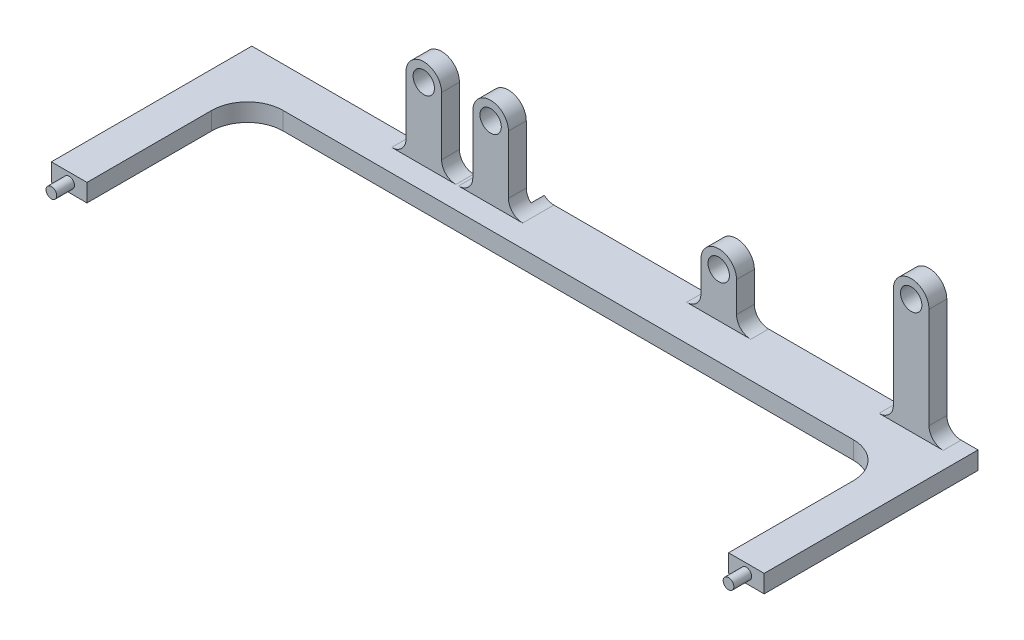
SolidWorks part; units mm, degrees
material "Alloy Steel"
ref_plane "Front Plane" through (0, 0, 0) normal (0, 0, 1) x (1, 0, 0)
ref_plane "Top Plane" through (0, 0, 0) normal (0, 1, 0) x (1, 0, 0)
ref_plane "Right Plane" through (0, 0, 0) normal (1, 0, 0) x (0, 0, -1)
sketch "Sketch1" plane through (0, 0, 0) normal (0, 1, 0) x (1, 0, 0)
  line L0 (-173.4223, 480) -> (-173.4223, 450)
  line L1 (-173.4223, 480) -> (800, 480)
  line L2 (-800, 450) -> (-800, -450)
  line L3 (-173.4223, -480) -> (800, -480)
  line L4 (800, 480) -> (800, -480)
  line L5 (0, 0) -> (800, -480) construction
  line L6 (-750, -450) -> (800, 480) construction
  line L7 (-173.4223, 450) -> (-800, 450)
  line L9 (0, 0) -> (-1738.6087, 0) construction
  line L11 (-173.4223, -450) -> (-800, -450)
  line L12 (-173.4223, -480) -> (-173.4223, -450)
  point P0 (0, 0)
  dimension "D1" = 960
  dimension "D3" = 30
extrude "Boss-Extrude1" add sketch "Sketch1" against normal blind 40
sketch "Sketch2" plane through (0, 0, 480) normal (0, 0, 1) x (1, 0, 0)
  line L0 (298, 0) -> (298, 100)
  line L1 (-173.4223, 0) -> (800, 0) construction
  line L2 (218, 0) -> (218, 100)
  line L3 (730, 0) -> (730, 258.2)
  line L4 (650, 0) -> (650, 258.2)
  line L5 (800, -40) -> (800, 0) construction
  arc A0 (218, 100) -> (298, 100) centre (258, 100) cw
  arc A1 (650, 258.2) -> (730, 258.2) centre (690, 258.2) cw
  circle A2 centre (258, 100) radius 24
  circle A3 centre (690, 258.2) radius 24
  dimension "D1" = 40
  dimension "D2" = 40
  dimension "D6" = 48
  dimension "D7" = 48
  dimension "D3" = 70
  dimension "D4" = 432
  dimension "D5" = 158.2
  dimension "D8" = 100
extrude "Boss-Extrude2" add sketch "Sketch2" against normal blind 40
sketch "Sketch3" plane through (0, 0, 450) normal (0, 0, 1) x (1, 0, 0)
  line L6 (-184, 0) -> (-184, 162.7)
  line L7 (-264, 0) -> (-264, 162.7)
  line L8 (-334, 0) -> (-334, 162.7)
  line L9 (-414, 0) -> (-414, 162.7)
  arc A4 (-264, 162.7) -> (-184, 162.7) centre (-224, 162.7) cw
  circle A5 centre (-224, 162.7) radius 24
  arc A6 (-414, 162.7) -> (-334, 162.7) centre (-374, 162.7) cw
  circle A7 centre (-374, 162.7) radius 24
  dimension "D11" = 150
  dimension "D12" = 48
  dimension "D13" = 40
mirror "Mirror1" about plane through (0, 0, 0) normal (0, 0, 1) of bodies 102
extrude "Boss-Extrude3" add sketch "Sketch3" against normal blind 40
mirror "Mirror2" about plane through (0, 0, 0) normal (0, 0, 1) of "Boss-Extrude3"
scale "Scale1" scale about centroid uniform scaling yes scale factor 0.125
fillet "Fillet3" radius 4 8 edges at (100.696, -9.9224, -57.5) (46.696, -9.9224, -57.5) (-13.554, -9.9224, -53.75) (-32.304, -9.9224, -53.75) (100.696, -9.9224, 57.5) (46.696, -9.9224, 57.5) (-13.554, -9.9224, 53.75) (-32.304, -9.9224, 53.75)
fillet "Fillet4" radius 4 8 edges at (-3.554, -9.9224, -53.75) (-22.304, -9.9224, -53.75) (56.696, -9.9224, -57.5) (110.696, -9.9224, -57.5) (110.696, -9.9224, 57.5) (56.696, -9.9224, 57.5) (-3.554, -9.9224, 53.75) (-22.304, -9.9224, 53.75)
sketch "Sketch4" plane through (0, -9.9224, 0) normal (0, 1, 0) x (1, 0, 0)
  line L0 (-70.554, 0) -> (109.446, 0) construction
  line L1 (-60.554, 45) -> (99.446, 45)
  line L2 (-70.554, 35) -> (-70.554, -35)
  line L3 (-60.554, -45) -> (99.446, -45)
  line L4 (109.446, 35) -> (109.446, -35)
  line L5 (119.446, -60) -> (119.446, 60) construction
  line L6 (-80.554, 56.25) -> (-80.554, -56.25) construction
  arc A0 (99.446, 45) -> (109.446, 35) centre (99.446, 35) cw
  arc A1 (99.446, -45) -> (109.446, -35) centre (99.446, -35) ccw
  arc A2 (-70.554, -35) -> (-60.554, -45) centre (-60.554, -35) ccw
  arc A3 (-60.554, 45) -> (-70.554, 35) centre (-60.554, 35) ccw
  point P8 (119.446, 0)
  point P9 (19.446, 0)
  point P12 (109.446, 45)
  point P17 (-70.554, -45)
  point P20 (-70.554, 45)
  dimension "D3" = 10
  dimension "D1" = 180
  dimension "D2" = 90
  dimension "D4" = 10
extrude "Cut-Extrude1" cut sketch "Sketch4" against normal through all both and the other way through all
sketch "Sketch5" plane through (0, -9.9224, 0) normal (0, 1, 0) x (1, 0, 0)
  line L0 (0, 0) -> (123.5098, 0)
  line L1 (123.5098, 0) -> (123.5098, -66.2129)
  line L2 (123.5098, -66.2129) -> (-94.641, -66.2129)
  line L3 (-94.641, -66.2129) -> (-94.641, 0)
  line L4 (-94.641, 0) -> (0, 0)
extrude "Cut-Extrude2" cut sketch "Sketch5" against normal through all both and the other way through all
sketch "Sketch6" plane through (0, 0, 0) normal (0, 0, 1) x (1, 0, 0)
  line L0 (-70.554, -9.9224) -> (-70.554, -14.9224) construction
  line L1 (-70.554, -9.9224) -> (-80.554, -9.9224) construction
  line L2 (119.446, -9.9224) -> (109.446, -9.9224) construction
  circle A0 centre (-75.554, -12.4224) radius 1.5
  circle A1 centre (114.446, -12.4224) radius 1.5
  point P2 (-82.4117, -3.8673)
  point P3 (-75.5505, -12.1943)
  point P6 (-70.554, -12.4224)
  point P7 (0, 0)
  point P10 (-75.554, -9.9224)
  point P13 (2.9084, -12.8642)
  point P14 (73.7476, -11.9773)
  point P15 (115.1753, -12.4224)
  point P16 (0, 0)
  point P19 (114.446, -9.9224)
  dimension "D1" = 3
extrude "Boss-Extrude4" add sketch "Sketch6" along normal blind 5
equation "\"2cmcm\"=4"
